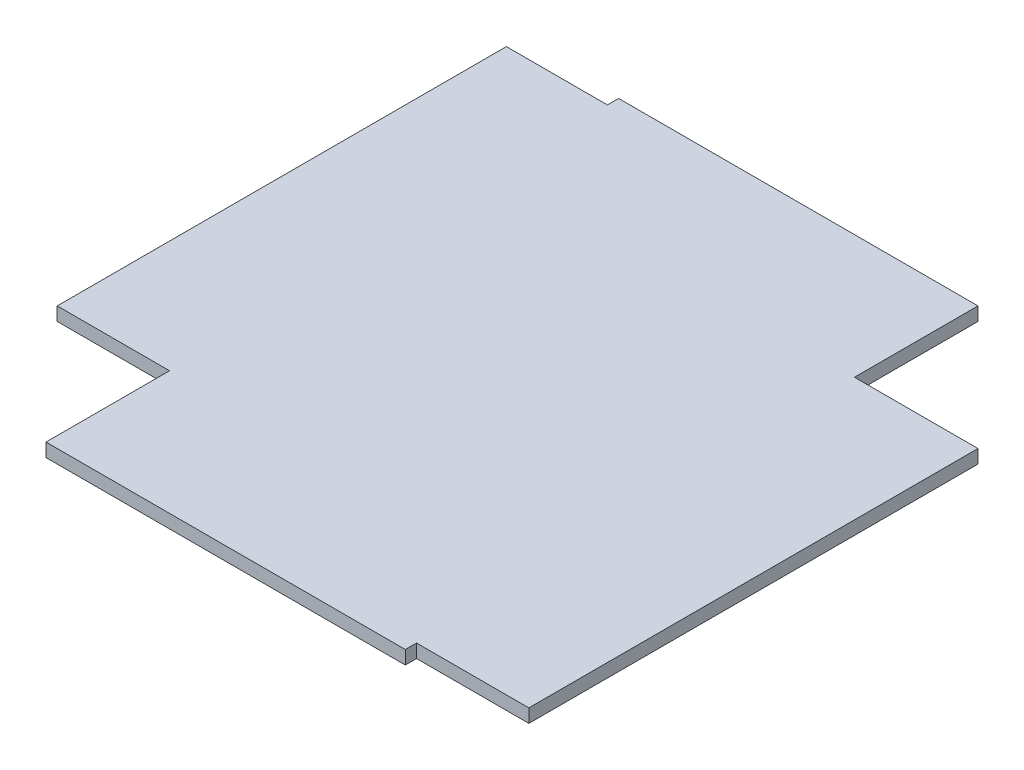
SolidWorks part; units mm, degrees
ref_plane "Front Plane" through (0, 0, 0) normal (0, 0, 1) x (1, 0, 0)
ref_plane "Top Plane" through (0, 0, 0) normal (0, 1, 0) x (1, 0, 0)
ref_plane "Right Plane" through (0, 0, 0) normal (1, 0, 0) x (0, 0, -1)
sketch "Sketch1" plane through (0, 0, 0) normal (0, 1, 0) x (1, 0, 0)
  line L1 (-75, 75) -> (75, 75)
  line L2 (-75, 75) -> (-75, -75)
  line L3 (-75, -75) -> (75, -75)
  line L4 (75, 75) -> (75, -75)
  line L5 (-75, 75) -> (75, -75) construction
  line L6 (-75, -75) -> (75, 75) construction
  point P0 (0, 0)
  dimension "D1" = 150
  dimension "D2" = 150
extrude "Boss-Extrude1" add sketch "Sketch1" along normal blind 6
sketch "Sketch2" plane through (0, 6, 0) normal (0, 1, 0) x (1, 0, 0)
  line L0 (75, 75) -> (-75, 75) construction
  line L1 (-75, -75) -> (75, -75) construction
  line L2 (-75, 75) -> (-75, -75) construction
  line L3 (75, -75) -> (75, 75) construction
  line L7 (-65, 65) -> (-5, 65)
  line L8 (-65, 65) -> (-5, 5)
  line L9 (-5, 5) -> (-5, 65)
  line L10 (65, 65) -> (5, 65)
  line L11 (5, 65) -> (5, 5)
  line L12 (5, 5) -> (65, 65)
  line L13 (65, -65) -> (5, -65)
  line L14 (5, -65) -> (5, -5)
  line L15 (5, -5) -> (65, -65)
  line L16 (-65, -65) -> (-5, -65)
  line L17 (-5, -65) -> (-5, -5)
  line L18 (-5, -5) -> (-65, -65)
  line L19 (65, 55) -> (5, -5)
  line L20 (5, -5) -> (65, -5)
  line L21 (65, -5) -> (65, 55)
  line L22 (5, 5) -> (65, 5)
  line L23 (65, 5) -> (65, -55)
  line L24 (65, -55) -> (5, 5)
  line L25 (-65, 55) -> (-65, -5)
  line L26 (-65, -5) -> (-5, -5)
  line L27 (-5, -5) -> (-65, 55)
  line L28 (-5, 5) -> (-65, 5)
  line L29 (-65, 5) -> (-65, -55)
  line L30 (-65, -55) -> (-5, 5)
  dimension "D1" = 60
  dimension "D2" = 45
  dimension "D3" = 0
  dimension "D4" = 10
  dimension "D5" = 60
  dimension "D6" = 60
  dimension "D7" = 45
  dimension "D8" = 45
  dimension "D9" = 60
  dimension "D10" = 10
  dimension "D11" = 0
  dimension "D12" = 60
  dimension "D13" = 45
  dimension "D14" = 20
  dimension "D15" = 60
  dimension "D16" = 45
  dimension "D17" = 60
  dimension "D18" = 45
  dimension "D19" = 10
  dimension "D20" = 20
  dimension "D21" = 10
  dimension "D22" = 0
  dimension "D23" = 10
extrude "Cut-Extrude2" cut sketch "Sketch2" against normal blind 6
sketch "Sketch3" plane through (0, 6, 0) normal (0, 1, 0) x (1, 0, 0)
  line L1 (75, 75) -> (130, 75)
  line L2 (75, 75) -> (75, -125)
  line L3 (75, -125) -> (130, -125)
  line L4 (130, 75) -> (130, -125)
  dimension "D1" = 200
  dimension "D2" = 55
extrude "Boss-Extrude3" add sketch "Sketch3" against normal blind 6
sketch "Sketch4" plane through (0, 6, 0) normal (0, 1, 0) x (1, 0, 0)
  line L0 (-75, -75) -> (75, -75) construction
  line L1 (80, -75) -> (-80, -75)
  line L2 (80, -75) -> (80, -130)
  line L3 (80, -130) -> (-80, -130)
  line L4 (-80, -75) -> (-80, -130)
  dimension "D1" = 160
  dimension "D2" = 55
  dimension "D3" = 55
extrude "Boss-Extrude4" add sketch "Sketch4" against normal blind 6
sketch "Sketch5" plane through (0, 6, 0) normal (0, 1, 0) x (1, 0, 0)
  line L0 (-75, 75) -> (-75, -75) construction
  line L1 (-75, -75) -> (-130, -75)
  line L2 (-75, -75) -> (-75, 125)
  line L3 (-75, 125) -> (-130, 125)
  line L4 (-130, -75) -> (-130, 125)
  line L5 (-80, -130) -> (80, -130) construction
  dimension "D1" = 55
  dimension "D2" = 200
  dimension "D3" = 55
extrude "Boss-Extrude5" add sketch "Sketch5" against normal blind 6
sketch "Sketch6" plane through (0, 6, 0) normal (0, 1, 0) x (1, 0, 0)
  line L0 (130, 75) -> (-75, 75) construction
  line L1 (-85, 75) -> (75, 75)
  line L2 (-85, 75) -> (-85, 130)
  line L3 (-85, 130) -> (75, 130)
  line L4 (75, 75) -> (75, 130)
  line L5 (130, -125) -> (130, 75) construction
  dimension "D1" = 55
  dimension "D2" = 160
  dimension "D3" = 55
extrude "Boss-Extrude6" add sketch "Sketch6" against normal blind 6
